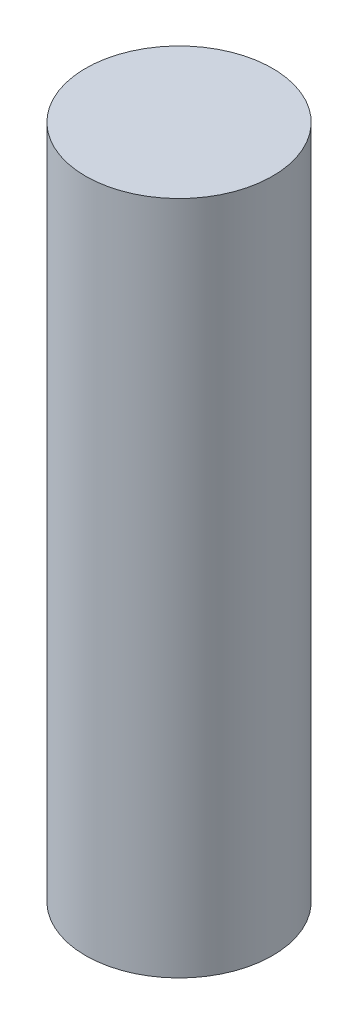
SolidWorks part; units mm, degrees
ref_plane "Front Plane" through (0, 0, 0) normal (0, 0, 1) x (1, 0, 0)
ref_plane "Top Plane" through (0, 0, 0) normal (0, 1, 0) x (1, 0, 0)
ref_plane "Right Plane" through (0, 0, 0) normal (1, 0, 0) x (0, 0, -1)
sketch "Sketch1" plane through (0, 0, 0) normal (0, 1, 0) x (1, 0, 0)
  circle A0 centre (0, 0) radius 9
  dimension "D1" = 18
extrude "Boss-Extrude1" add sketch "Sketch1" along normal blind 65
